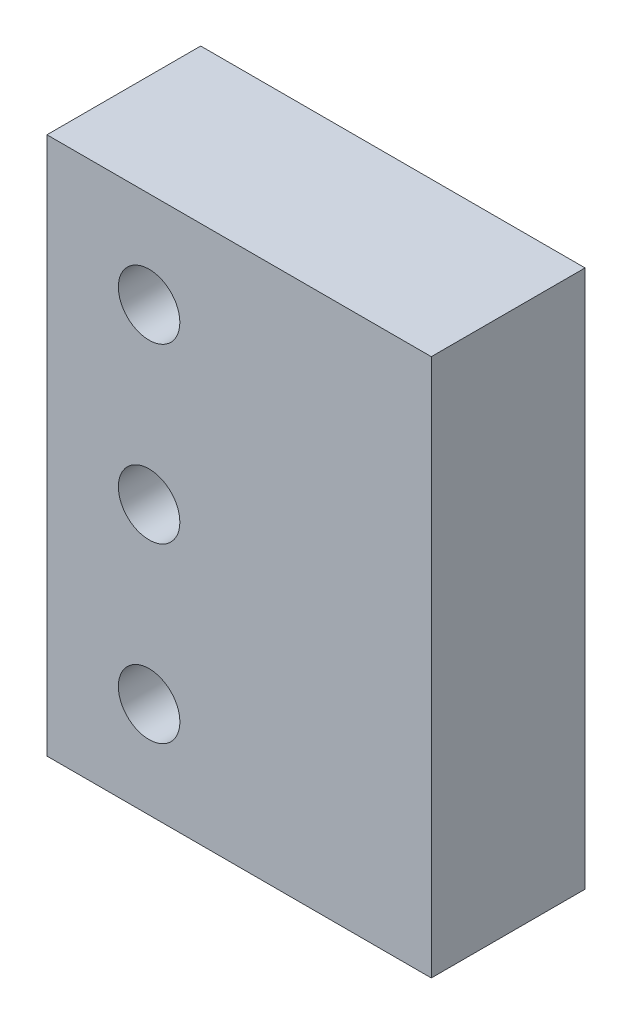
SolidWorks part; units mm, degrees
material "Plain Carbon Steel"
ref_plane "Front Plane" through (0, 0, 0) normal (0, 0, 1) x (1, 0, 0)
ref_plane "Top Plane" through (0, 0, 0) normal (0, 1, 0) x (1, 0, 0)
ref_plane "Right Plane" through (0, 0, 0) normal (1, 0, 0) x (0, 0, -1)
sketch "Sketch1" plane through (0, 0, 0) normal (0, 0, 1) x (1, 0, 0)
  line L0 (0, 0) -> (-48.9328, 0) construction
  line L5 (-25, -35) -> (25, -35)
  line L6 (-25, -35) -> (-25, 35)
  line L7 (-25, 35) -> (25, 35)
  line L8 (25, -35) -> (25, 35)
  line L9 (-25, -35) -> (25, 35) construction
  line L10 (-25, 35) -> (25, -35) construction
  circle A0 centre (-11.7121, 0) radius 4
  circle A1 centre (-11.7121, 22.5) radius 4
  circle A2 centre (-11.7121, -22.5) radius 4
  point P0 (0, 0)
  point P14 (0, 0)
  dimension "D3" = 45
  dimension "D4" = 13.2879
  dimension "D5" = 8
  dimension "D1" = 70
  dimension "D2" = 50
extrude "Boss-Extrude1" add sketch "Sketch1" along normal mid plane 20
